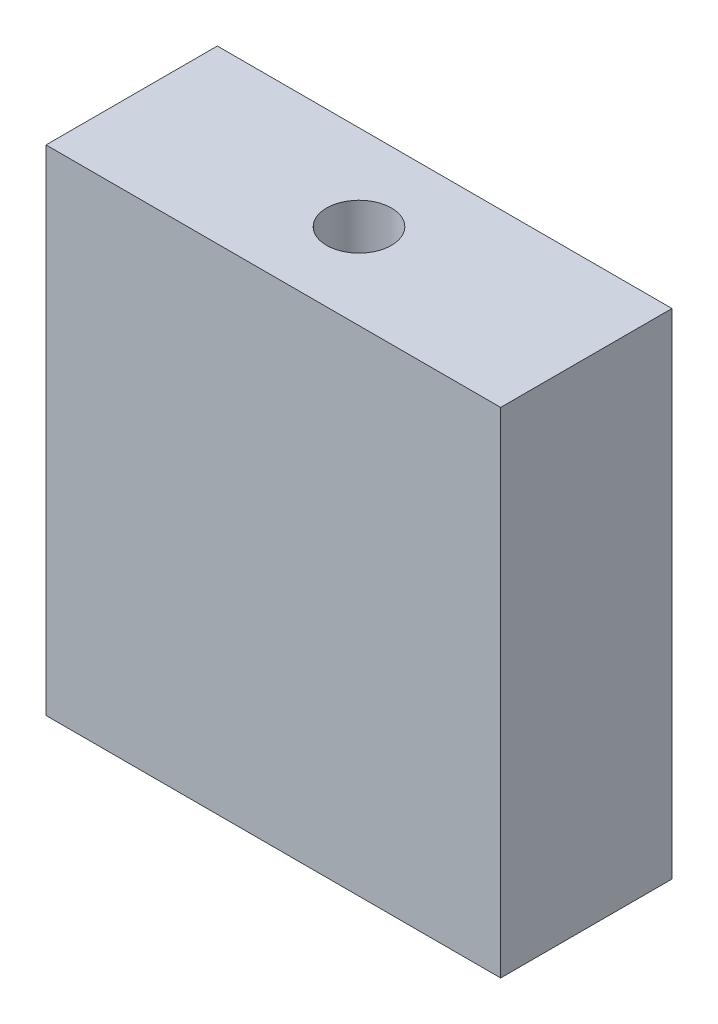
SolidWorks part; units mm, degrees
ref_plane "Front Plane" through (0, 0, 0) normal (0, 0, 1) x (1, 0, 0)
ref_plane "Top Plane" through (0, 0, 0) normal (0, 1, 0) x (1, 0, 0)
ref_plane "Right Plane" through (0, 0, 0) normal (1, 0, 0) x (0, 0, -1)
sketch "Sketch1" plane through (0, 0, 0) normal (0, 0, 1) x (1, 0, 0)
  line L1 (8.763, -9.525) -> (-8.763, -9.525)
  line L2 (8.763, -9.525) -> (8.763, 9.525)
  line L3 (8.763, 9.525) -> (-8.763, 9.525)
  line L4 (-8.763, -9.525) -> (-8.763, 9.525)
  line L5 (8.763, -9.525) -> (-8.763, 9.525) construction
  line L6 (8.763, 9.525) -> (-8.763, -9.525) construction
  point P0 (0, 0)
  dimension "D1" = 19.05
  dimension "D2" = 17.526
extrude "Boss-Extrude1" add sketch "Sketch1" along normal blind 6.604
hole_wizard "M3x0.5 Tapped Hole1" positions "Sketch2" profile "Sketch3" tap size "M3x0.5" standard "ANSI Metric"
sketch "Sketch2" plane through (0, 9.525, 0) normal (0, 1, 0) x (1, 0, 0)
  line L0 (-8.763, -3.302) -> (8.763, -3.302) construction
  line L1 (-8.763, -6.604) -> (-8.763, 0) construction
  line L2 (8.763, -6.604) -> (8.763, 0) construction
  point P9 (0, -3.302)
sketch "Sketch3" plane through (0, 9.525, 3.302) normal (1, 0, 0) x (0, 0, 1)
  line L0 (0, 0) -> (0, 8.2441)
  line L1 (0, 8.2441) -> (1.25, 7.493)
  line L2 (1.25, 7.493) -> (1.25, 0)
  line L5 (1.25, 0) -> (0, 0)
  line L10 (0, 8.2441) -> (-1.25, 7.493) construction
  line L11 (0, -6.35) -> (0, 107.95) construction
  dimension "Tap Drill Dia." = 2.5
  dimension "Tap Drill Depth" = 7.493
  dimension "Drill Angle" = 118
cosmetic thread "Hole Thread1" parameters "D1"=5.9944, "D2"=3
hole_wizard "M3x0.5 Tapped Hole2" positions "Sketch4" profile "Sketch5" tap size "M3x0.5" standard "ANSI Metric"
sketch "Sketch4" plane through (0, -9.525, 0) normal (0, -1, 0) x (-1, 0, 0)
  line L0 (-8.763, -3.302) -> (8.763, -3.302) construction
  line L1 (-8.763, -6.604) -> (-8.763, 0) construction
  line L2 (8.763, -6.604) -> (8.763, 0) construction
  point P9 (0, -3.302)
sketch "Sketch5" plane through (0, -9.525, 3.302) normal (1, 0, 0) x (0, 0, -1)
  line L0 (0, 0) -> (0, 8.2441)
  line L1 (0, 8.2441) -> (1.25, 7.493)
  line L2 (1.25, 7.493) -> (1.25, 0)
  line L5 (1.25, 0) -> (0, 0)
  line L10 (0, 8.2441) -> (-1.25, 7.493) construction
  line L11 (0, -6.35) -> (0, 107.95) construction
  dimension "Tap Drill Dia." = 2.5
  dimension "Tap Drill Depth" = 7.493
  dimension "Drill Angle" = 118
cosmetic thread "Hole Thread2"
